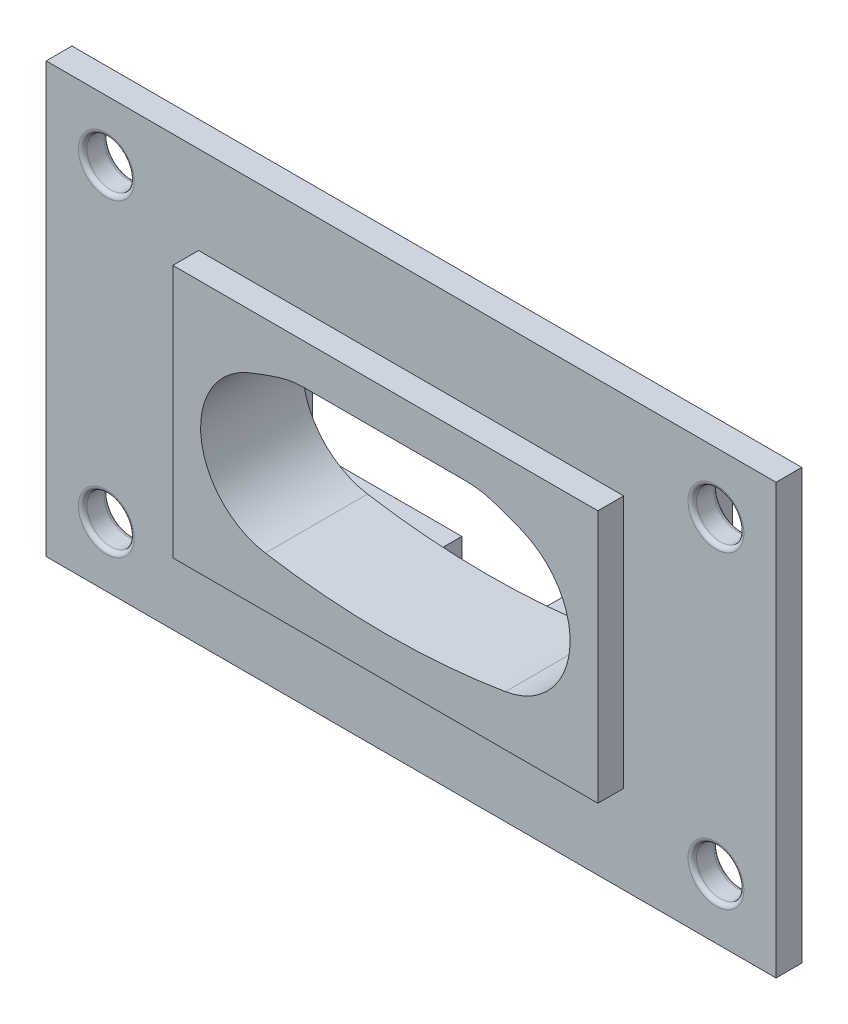
SolidWorks part; units mm, degrees
ref_plane "Front Plane" through (0, 0, 0) normal (0, 0, 1) x (1, 0, 0)
ref_plane "Top Plane" through (0, 0, 0) normal (0, 1, 0) x (1, 0, 0)
ref_plane "Right Plane" through (0, 0, 0) normal (1, 0, 0) x (0, 0, -1)
sketch "Sketch1" plane through (0, 0, 0) normal (0, 0, 1) x (1, 0, 0)
  line L0 (-12.5, 0) -> (12.5, 0) construction
  line L1 (0, 0) -> (0, 7868.0279) construction
  line L2 (-25.5, -13) -> (25.5, -13)
  line L3 (-25.5, -13) -> (-25.5, 13)
  line L4 (-25.5, 13) -> (25.5, 13)
  line L5 (25.5, -13) -> (25.5, 13)
  line L6 (-25.5, -13) -> (25.5, 13) construction
  line L7 (-25.5, 13) -> (25.5, -13) construction
  circle A0 centre (-12.5, 0) radius 8 construction
  circle A1 centre (12.5, 0) radius 8 construction
  arc A2 (-15.9979, 8.3) -> (-13.9784, -8.8807) centre (-12.518, 0) ccw
  arc A3 (15.9979, 8.3) -> (13.9784, -8.8807) centre (12.518, 0) cw
  arc A4 (-13.9784, -8.8807) -> (13.9784, -8.8807) centre (0, 76.121) ccw
  arc A5 (-15.9979, 8.3) -> (15.9979, 8.3) centre (0, -29.8571) cw
  point P4 (0, 0)
  point P11 (0, 0)
  point P17 (0, 11.518)
  dimension "D2" = 16
  dimension "D1" = 25
  dimension "D3" = 51
  dimension "D4" = 26
  dimension "D5" = 11.518
extrude "Boss-Extrude1" add sketch "Sketch1" along normal blind 5.9
sketch "Sketch3" plane through (0, 0, 5.9) normal (0, 0, 1) x (1, 0, 0)
  line L0 (0, 0) -> (0, 50000) construction
  line L1 (-42.5, -25) -> (42.5, -25)
  line L2 (-42.5, -25) -> (-42.5, 25)
  line L3 (-42.5, 25) -> (42.5, 25)
  line L4 (42.5, -25) -> (42.5, 25)
  line L5 (-42.5, -25) -> (42.5, 25) construction
  line L6 (-42.5, 25) -> (42.5, -25) construction
  line L7 (0, 0) -> (50000, 0) construction
  circle A0 centre (-35.5, 18) radius 2.75
  circle A1 centre (35.5, 18) radius 2.75
  circle A2 centre (35.5, -18) radius 2.75
  circle A3 centre (-35.5, -18) radius 2.75
  arc A4 (-13.9784, -8.8807) -> (13.9784, -8.8807) centre (0, 76.121) ccw construction
  arc A5 (13.9784, -8.8807) -> (15.9979, 8.3) centre (12.518, 0) ccw construction
  arc A6 (15.9979, 8.3) -> (-15.9979, 8.3) centre (0, -29.8571) ccw construction
  arc A7 (-15.9979, 8.3) -> (-13.9784, -8.8807) centre (-12.518, 0) ccw construction
  arc A8 (-13.9784, -8.8807) -> (13.9784, -8.8807) centre (0, 76.121) ccw
  arc A9 (13.9784, -8.8807) -> (15.9979, 8.3) centre (12.518, 0) ccw
  arc A10 (15.9979, 8.3) -> (-15.9979, 8.3) centre (0, -29.8571) ccw
  arc A11 (-15.9979, 8.3) -> (-13.9784, -8.8807) centre (-12.518, 0) ccw
  point P0 (0, 0)
  dimension "D3" = 5.5
  dimension "D1" = 85
  dimension "D2" = 50
  dimension "D4" = 7
  dimension "D5" = 7
extrude "Boss-Extrude2" add sketch "Sketch3" along normal blind 3
sketch "Sketch4" plane through (0, 0, 8.9) normal (0, 0, 1) x (1, 0, 0)
  line L1 (-24.75, -14.75) -> (24.75, -14.75)
  line L2 (-24.75, -14.75) -> (-24.75, 14.75)
  line L3 (-24.75, 14.75) -> (24.75, 14.75)
  line L4 (24.75, -14.75) -> (24.75, 14.75)
  line L5 (-24.75, -14.75) -> (24.75, 14.75) construction
  line L6 (-24.75, 14.75) -> (24.75, -14.75) construction
  arc A0 (-13.9784, -8.8807) -> (13.9784, -8.8807) centre (0, 76.121) ccw construction
  arc A1 (13.9784, -8.8807) -> (15.9979, 8.3) centre (12.518, 0) ccw construction
  arc A2 (15.9979, 8.3) -> (-15.9979, 8.3) centre (0, -29.8571) ccw construction
  arc A3 (-15.9979, 8.3) -> (-13.9784, -8.8807) centre (-12.518, 0) ccw construction
  arc A4 (-13.9784, -8.8807) -> (13.9784, -8.8807) centre (0, 76.121) ccw
  arc A5 (13.9784, -8.8807) -> (15.9979, 8.3) centre (12.518, 0) ccw
  arc A6 (15.9979, 8.3) -> (-15.9979, 8.3) centre (0, -29.8571) ccw
  arc A7 (-15.9979, 8.3) -> (-13.9784, -8.8807) centre (-12.518, 0) ccw
  point P0 (0, 0)
  dimension "D1" = 49.5
  dimension "D2" = 29.5
extrude "Boss-Extrude3" add sketch "Sketch4" along normal blind 3
fillet "Fillet1" radius 0.5 8 edges at (-38.25, -18, 5.9) (-38.25, -18, 8.9) (38.25, -18, 5.9) (38.25, -18, 8.9) (32.75, 18, 5.9) (32.75, 18, 8.9) (-32.75, 18, 5.9) (-32.75, 18, 8.9)
sketch "Sketch6" plane through (0, 0, 0) normal (0, 0, -1) x (-1, 0, 0)
  line L0 (-10.8501, 10.07) -> (10.8501, 10.07)
  line L1 (-25.5, 13) -> (25.5, 13) construction
  arc A0 (15.9979, 8.3) -> (-15.9979, 8.3) centre (0, -29.8571) ccw construction
  arc A1 (10.8501, 10.07) -> (-10.8501, 10.07) centre (0, -29.8571) ccw
  dimension "D1" = 2.93
extrude "Boss-Extrude4" add sketch "Sketch6" against normal up to surface (11.9 mm away) up to face at (0, 0, 11.9)
fillet "Fillet2" radius 10 2 edges at (-10.8501, 10.07, 5.95) (10.8501, 10.07, 5.95)
sketch "Sketch7" plane through (0, 0, 0) normal (0, 0, -1) x (-1, 0, 0)
  line L0 (0, 0) -> (50000, 0) construction
  line L1 (-22.86, -10.16) -> (22.86, -10.16) construction
  line L2 (-22.86, -10.16) -> (-22.86, 10.16) construction
  line L3 (-22.86, 10.16) -> (22.86, 10.16) construction
  line L4 (22.86, -10.16) -> (22.86, 10.16) construction
  line L5 (-22.86, -10.16) -> (22.86, 10.16) construction
  line L6 (-22.86, 10.16) -> (22.86, -10.16) construction
  line L7 (0, 0) -> (0, 50000) construction
  line L8 (-23.36, 10.66) -> (23.36, 10.66)
  line L9 (23.36, -10.66) -> (23.36, 10.66)
  line L10 (-23.36, -10.66) -> (-6, -10.66)
  line L11 (-23.36, -10.66) -> (-23.36, 10.66)
  line L12 (-6, -10.66) -> (-6, -13)
  line L13 (6, -10.66) -> (6, -13)
  line L14 (6, -10.66) -> (23.36, -10.66)
  line L15 (-23.36, -10.66) -> (23.36, -10.66) construction
  line L16 (-25.5, 13) -> (-25.5, -13)
  line L17 (-25.5, -13) -> (25.5, -13)
  line L18 (25.5, -13) -> (25.5, 13)
  line L19 (25.5, 13) -> (-25.5, 13)
  line L20 (-25.5, 13) -> (-25.5, -13)
  line L21 (-25.5, -13) -> (-6, -13)
  line L22 (25.5, -13) -> (25.5, 13)
  line L23 (25.5, 13) -> (-25.5, 13)
  point P0 (0, 0)
  line M11 (-25.5, 13) -> (-25.5, -13)
  line M12 (-25.5, -13) -> (25.5, -13)
  line M13 (25.5, -13) -> (25.5, 13)
  line M14 (25.5, 13) -> (-25.5, 13)
  dimension "D3" = 0.5
  dimension "D4" = 0
  dimension "D1" = 45.72
  dimension "D2" = 20.32
  dimension "D5" = 6
extrude "Boss-Extrude5" add sketch "Sketch7" along normal blind 3 contours L14 L13 L12 L10 L11 L8 L9 M12 M13 M14 M11
fillet "Fillet3" radius 1 2 edges at (-6, -11.83, 0) (6, -11.83, 0)
